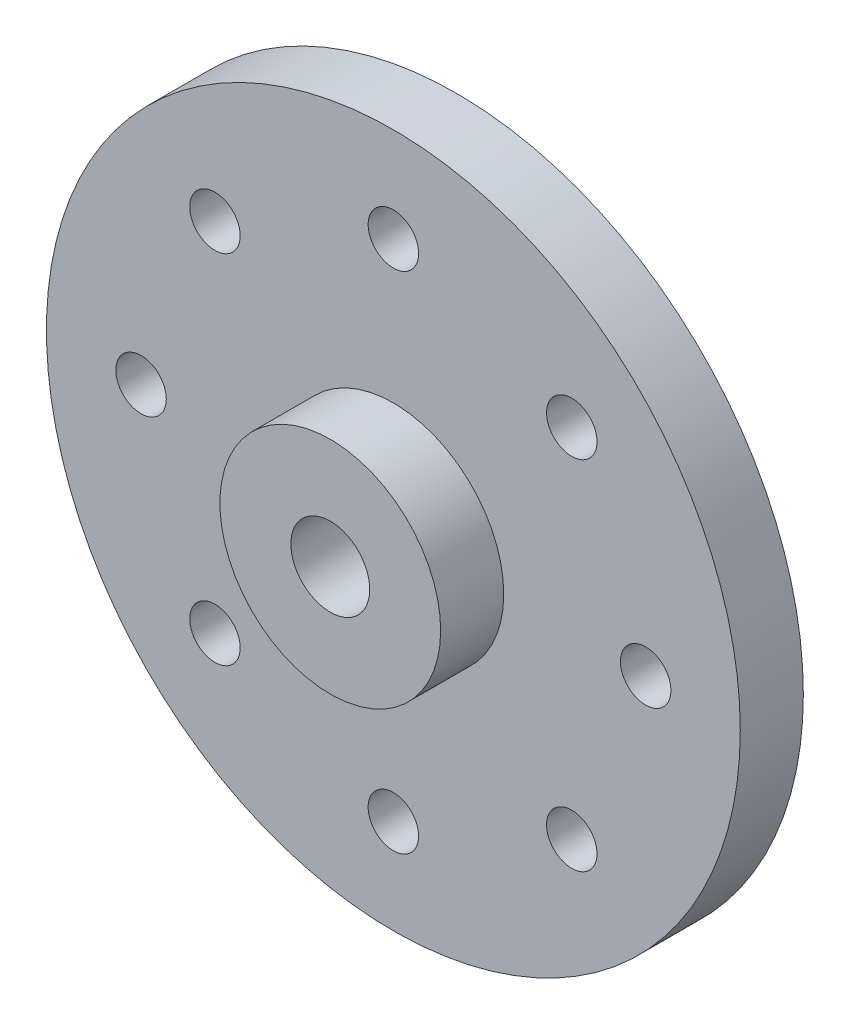
SolidWorks part; units mm, degrees
material "2024 Alloy (SN)"
ref_plane "Front Plane" through (0, 0, 0) normal (0, 0, 1) x (1, 0, 0)
ref_plane "Top Plane" through (0, 0, 0) normal (0, 1, 0) x (1, 0, 0)
ref_plane "Right Plane" through (0, 0, 0) normal (1, 0, 0) x (0, 0, -1)
sketch "Sketch1" plane through (0, 0, 0) normal (0, 0, 1) x (1, 0, 0)
  circle A0 centre (0, 0) radius 11
  dimension "D1" = 22
extrude "Boss-Extrude1" add sketch "Sketch1" along normal blind 2
sketch "Sketch2" plane through (0, 0, 2) normal (0, 0, 1) x (1, 0, 0)
  circle A0 centre (0, 8) radius 0.782
  circle A1 centre (5.6569, 5.6569) radius 0.782
  circle A2 centre (8, 0) radius 0.782
  circle A3 centre (5.6569, -5.6569) radius 0.782
  circle A4 centre (0, -8) radius 0.782
  circle A5 centre (-5.6569, -5.6569) radius 0.782
  circle A6 centre (-8, 0) radius 0.782
  circle A7 centre (-5.6569, 5.6569) radius 0.782
  dimension "D1" = 8
  dimension "D2" = 8
sketch "Sketch3" plane through (0, 0, 2) normal (0, 0, 1) x (1, 0, 0)
  circle A0 centre (0, 0) radius 3.5
  dimension "D1" = 7
extrude "Boss-Extrude2" add sketch "Sketch3" along normal blind 2
hole_wizard "M2x0.4 Tapped Hole1" positions "Sketch5" profile "Sketch4" tap size "M2x0.4" standard "Ansi Metric"
sketch "Sketch5" plane through (0, 0, 2) normal (0, 0, 1) x (1, 0, 0)
  point P0 (0, 8)
  point P1 (-5.6569, 5.6569)
  point P4 (-8, 0)
  point P7 (-5.6569, -5.6569)
  point P10 (0, -8)
  point P13 (5.6569, -5.6569)
  point P16 (8, 0)
  point P19 (5.6569, 5.6569)
sketch "Sketch4" plane through (0, 8, 2) normal (1, 0, 0) x (0, -1, 0)
  line L0 (0, 0) -> (0, 5.6807)
  line L1 (0, 5.6807) -> (0.8, 5.2)
  line L2 (0.8, 5.2) -> (0.8, 0)
  line L5 (0.8, 0) -> (0, 0)
  line L10 (0, 5.6807) -> (-0.8, 5.2) construction
  line L11 (0, -6.35) -> (0, 107.95) construction
  dimension "Tap Drill Dia." = 1.6
  dimension "Tap Drill Depth" = 5.2
  dimension "Drill Angle" = 118
cosmetic thread "Hole Thread1" parameters "D1"=2, "D2"=2
cosmetic thread "Hole Thread2" parameters "D1"=2, "D2"=2
cosmetic thread "Hole Thread3" parameters "D1"=2, "D2"=2
cosmetic thread "Hole Thread4" parameters "D1"=2, "D2"=2
cosmetic thread "Hole Thread5" parameters "D1"=2, "D2"=2
cosmetic thread "Hole Thread6" parameters "D1"=2, "D2"=2
cosmetic thread "Hole Thread7" parameters "D1"=2, "D2"=2
cosmetic thread "Hole Thread8" parameters "D1"=2, "D2"=2
sketch "Sketch8" plane through (0, 0, 0) normal (0, 0, -1) x (-1, 0, 0)
  circle A0 centre (0, 0) radius 1.25
  circle A1 centre (0, 0) radius 2
  dimension "D1" = 4
extrude "Boss-Extrude3" add sketch "Sketch8" along normal blind 1
hole_wizard "M3x0.5 Tapped Hole1" positions "Sketch7" profile "Sketch6" tap size "M3x0.5" standard "Ansi Metric"
sketch "Sketch7" plane through (0, 0, 4) normal (0, 0, 1) x (1, 0, 0)
  point P0 (0, 0)
sketch "Sketch6" plane through (0, 0, 4) normal (1, 0, 0) x (0, -1, 0)
  line L0 (0, 0) -> (0, 8.2511)
  line L1 (0, 8.2511) -> (1.25, 7.5)
  line L2 (1.25, 7.5) -> (1.25, 0)
  line L5 (1.25, 0) -> (0, 0)
  line L10 (0, 8.2511) -> (-1.25, 7.5) construction
  line L11 (0, -6.35) -> (0, 107.95) construction
  dimension "Tap Drill Dia." = 2.5
  dimension "Tap Drill Depth" = 7.5
  dimension "Drill Angle" = 118
cosmetic thread "Hole Thread9" parameters "D1"=4, "D2"=3
